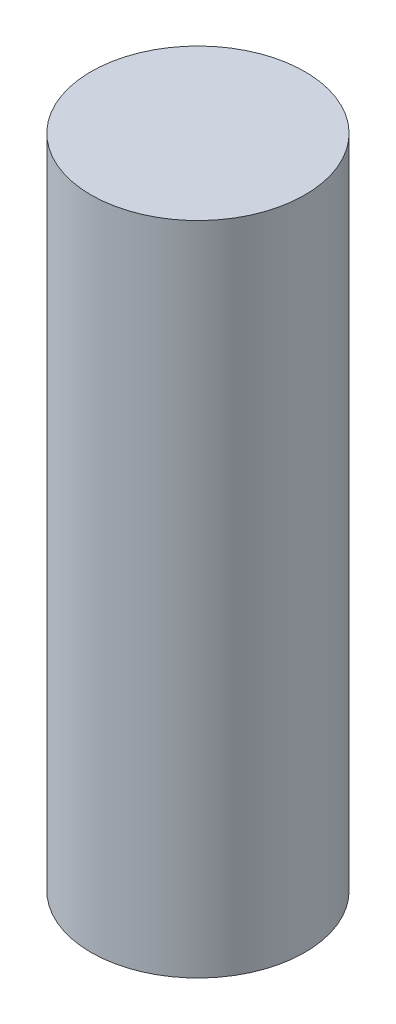
SolidWorks part; units mm, degrees
ref_plane "정면" through (0, 0, 0) normal (0, 0, 1) x (1, 0, 0)
ref_plane "윗면" through (0, 0, 0) normal (0, 1, 0) x (1, 0, 0)
ref_plane "우측면" through (0, 0, 0) normal (1, 0, 0) x (0, 0, -1)
sketch "스케치1" plane through (0, 0, 0) normal (0, 1, 0) x (1, 0, 0)
  circle A0 centre (0, 0) radius 2.2
  dimension "D1" = 4.4
extrude "보스-돌출1" add sketch "스케치1" along normal blind 13.5
